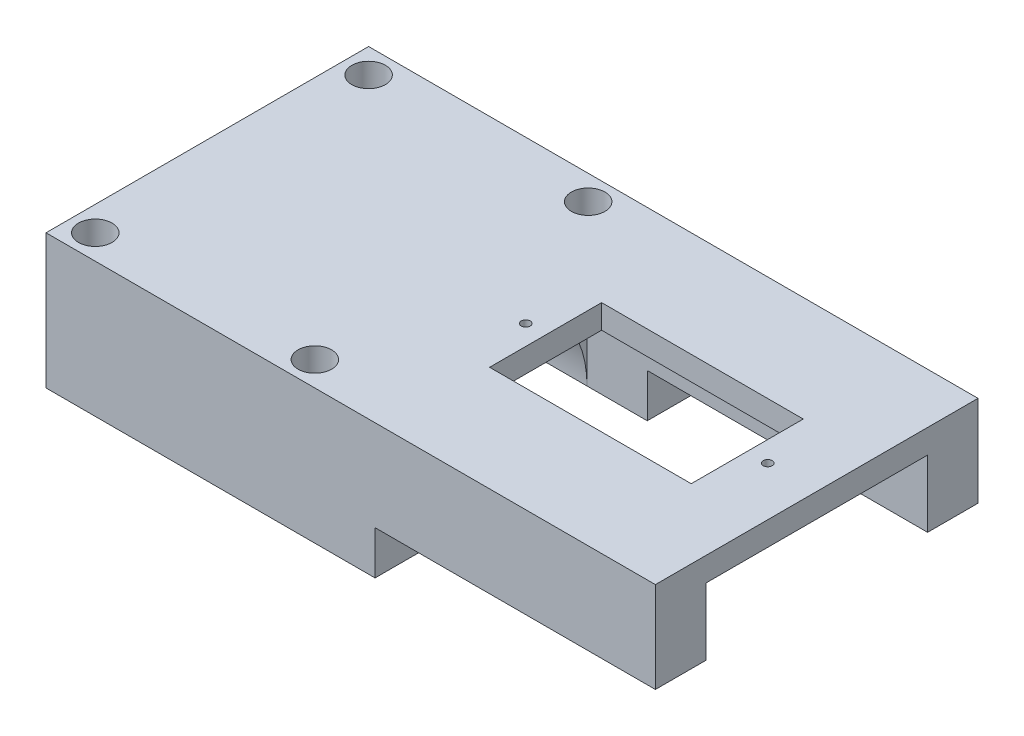
SolidWorks part; units mm, degrees
ref_plane "Front Plane" through (0, 0, 0) normal (0, 0, 1) x (1, 0, 0)
ref_plane "Top Plane" through (0, 0, 0) normal (0, 1, 0) x (1, 0, 0)
ref_plane "Right Plane" through (0, 0, 0) normal (1, 0, 0) x (0, 0, -1)
sketch "Sketch1" plane through (0, 0, 0) normal (0, 1, 0) x (1, 0, 0)
  line L1 (-15, -18) -> (15, -18)
  line L2 (-15, -18) -> (-15, 18)
  line L3 (-15, 18) -> (15, 18)
  line L4 (15, -18) -> (15, 18)
  line L5 (-15, -18) -> (15, 18) construction
  line L6 (-15, 18) -> (15, -18) construction
  point P0 (0, 0)
  dimension "D1" = 30
  dimension "D2" = 36
extrude "Boss-Extrude1" add sketch "Sketch1" along normal blind 30
sketch "Sketch3" plane through (15, 0, 0) normal (1, 0, 0) x (0, 0, -1)
  line L0 (0, 0) -> (0, 30) construction
  line L1 (-18, 0) -> (18, 0) construction
  line L2 (-18, 30) -> (18, 30) construction
  circle A0 centre (0, 15) radius 12.375
  dimension "D1" = 24.75
extrude "Cut-Extrude1" cut sketch "Sketch3" against normal blind 40
sketch "Sketch5" plane through (0, 30, 0) normal (0, 1, 0) x (1, 0, 0)
  line L7 (15, 18) -> (-15, 18) construction
  line L9 (-15, 18) -> (-15, -18) construction
  line L10 (0, 0) -> (0, 2.7791) construction
  line L11 (0, 2.7791) -> (0, 0) construction
  line L12 (0, 0) -> (-2.7536, 0) construction
  circle A1 centre (-12.25, 15.25) radius 1.875
  circle A2 centre (-12.25, -15.25) radius 1.875
  circle A3 centre (12.25, -15.25) radius 1.875
  circle A4 centre (12.25, 15.25) radius 1.875
  point P0 (0, 0)
  dimension "D2" = 3.75
  dimension "D3" = 2.75
  dimension "D4" = 2.75
extrude "Cut-Extrude2" cut sketch "Sketch5" against normal blind 40
sketch "Sketch7" plane through (0, 0, 0) normal (1, 0, 0) x (0, 0, -1)
  line L0 (-18, 30) -> (-18, 0) construction
  line L1 (-18, 15) -> (18, 15)
  line L2 (-18, 15) -> (-18, 0)
  line L3 (-18, 0) -> (18, 0)
  line L4 (18, 15) -> (18, 0)
extrude "Cut-Extrude3" cut sketch "Sketch7" against normal through all from surface at 15 starting at face at (15, 15, -12.375)
sketch "Sketch8" plane through (15, 0, 0) normal (1, 0, 0) x (0, 0, -1)
  line L0 (18, 30) -> (18, 15) construction
  line L1 (-18, 30) -> (18, 30)
  line L2 (-18, 30) -> (-18, 27.3314)
  line L3 (-12.375, 27.3314) -> (12.375, 27.3314)
  line L4 (18, 30) -> (18, 27.3314)
  line L5 (-12.375, 15) -> (-18, 15) construction
  line L6 (-18, 15) -> (-12.375, 15)
  line L7 (-18, 15) -> (-18, 27.3314)
  line L9 (-12.375, 15) -> (-12.375, 27.3314)
  line L12 (18, 27.3314) -> (18, 15)
  line L13 (18, 15) -> (12.375, 15)
  line L14 (12.375, 27.3314) -> (12.375, 15)
  arc A0 (12.375, 15) -> (-12.375, 15) centre (0, 15) ccw construction
  dimension "D1" = 5.625
extrude "Boss-Extrude2" add sketch "Sketch8" along normal blind 38
sketch "Sketch9" plane through (0, 30, 0) normal (0, 1, 0) x (1, 0, 0)
  line L0 (15, 0) -> (53, 0) construction
  line L1 (53, 18) -> (53, -18) construction
  line L2 (15, 18) -> (15, 0) construction
  line L3 (53, 18) -> (-15, 18) construction
  line L4 (-15, -18) -> (53, -18) construction
  line L5 (-15, 18) -> (-15, -18) construction
  line L13 (22.75, -6.25) -> (45.25, -6.25)
  line L24 (22.75, -6.25) -> (22.75, 6.25)
  line L25 (22.75, 6.25) -> (45.25, 6.25)
  line L30 (45.25, -6.25) -> (45.25, 6.25)
  line L31 (22.75, -6.25) -> (45.25, 6.25) construction
  line L35 (22.75, 6.25) -> (45.25, -6.25) construction
  line L36 (15, 0) -> (15, -18) construction
  circle A4 centre (20.5328, 0) radius 0.5
  circle A5 centre (47.5328, 0) radius 0.5
  point P0 (34, 0)
  dimension "D4" = 1
  dimension "D6" = 1
  dimension "D1" = 30
  dimension "D3" = 12.5
  dimension "D5" = 27
  dimension "22.5" = 22.5
extrude "Cut-Extrude4" cut sketch "Sketch9" against normal blind 10
sketch "Sketch10" plane through (0, 0, 12.375) normal (0, 0, -1) x (-1, 0, 0)
  line L7 (-53, 15) -> (-21.7187, 15)
  line L8 (-53, 15) -> (-53, 19.8617)
  line L9 (-53, 19.8617) -> (-21.7187, 19.8617)
  line L10 (-21.7187, 15) -> (-21.7187, 19.8617)
extrude "Cut-Extrude6" cut sketch "Sketch10" against normal through all both and the other way through all
